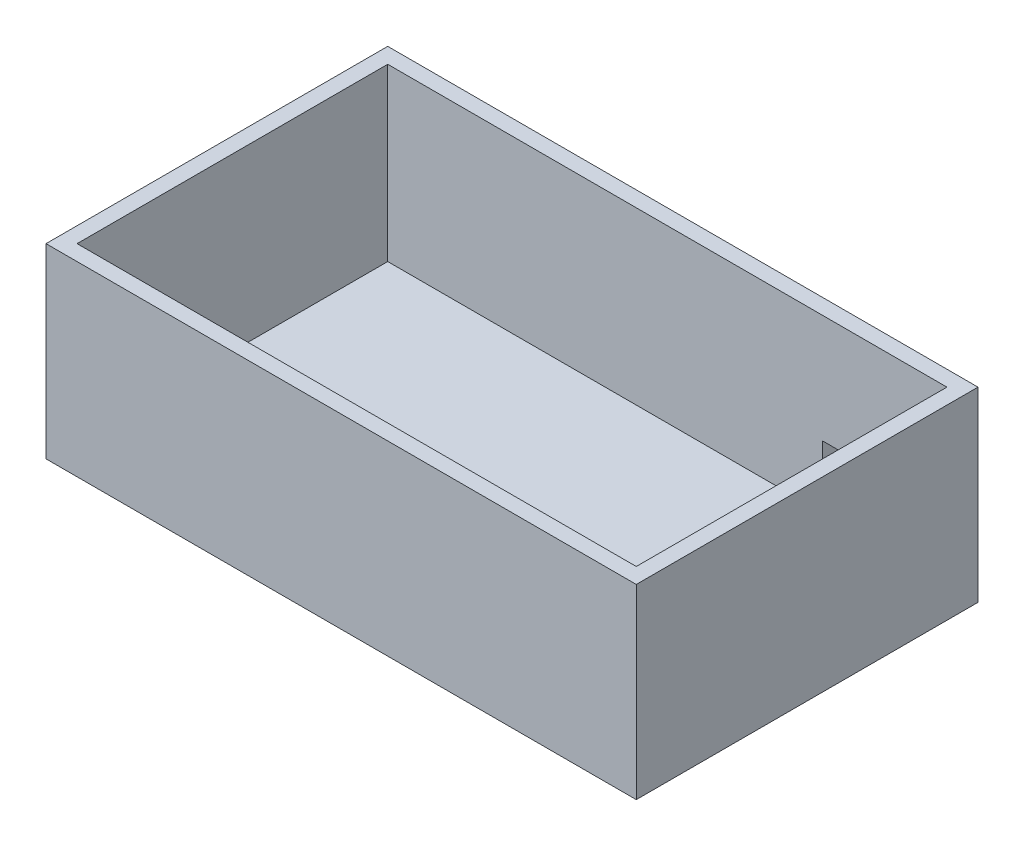
SolidWorks part; units mm, degrees
ref_plane "Front Plane" through (0, 0, 0) normal (0, 0, 1) x (1, 0, 0)
ref_plane "Top Plane" through (0, 0, 0) normal (0, 1, 0) x (1, 0, 0)
ref_plane "Right Plane" through (0, 0, 0) normal (1, 0, 0) x (0, 0, -1)
sketch "Sketch1" plane through (0, 0, 0) normal (0, 1, 0) x (1, 0, 0)
  line L0 (-5, 105) -> (185, 105)
  line L1 (0, 0) -> (180, 0)
  line L2 (0, 0) -> (0, 100)
  line L3 (0, 100) -> (180, 100)
  line L4 (180, 0) -> (180, 100)
  line L5 (185, -5) -> (185, 105)
  line L6 (-5, -5) -> (185, -5)
  line L7 (-5, -5) -> (-5, 105)
  dimension "D1" = 180
  dimension "D2" = 100
  dimension "D3" = 5
extrude "Boss-Extrude1" add sketch "Sketch1" along normal blind 60
sketch "Sketch2" plane through (185, 0, 0) normal (1, 0, 0) x (0, 0, -1)
  line L0 (105, 60) -> (105, 0) construction
  line L1 (-5, 0) -> (105, 0)
  line L2 (-5, 0) -> (-5, 5)
  line L3 (-5, 5) -> (105, 5)
  line L4 (105, 0) -> (105, 5)
  dimension "D1" = 5
extrude "Boss-Extrude2" add sketch "Sketch2" against normal up to surface (190 mm away) up to face at (-5, 30, -50)
sketch "Sketch3" plane through (0, 0, -105) normal (0, 0, -1) x (-1, 0, 0)
  line L0 (-185, 60) -> (-185, 0) construction
  line L1 (-165, 25) -> (-140, 25)
  line L2 (-165, 25) -> (-165, 5)
  line L3 (-165, 5) -> (-140, 5)
  line L4 (-140, 25) -> (-140, 5)
  line L5 (-185, 0) -> (5, 0) construction
  dimension "D1" = 20
  dimension "D2" = 5
  dimension "D3" = 20
  dimension "D4" = 25
extrude "Cut-Extrude1" cut sketch "Sketch3" against normal blind 60
